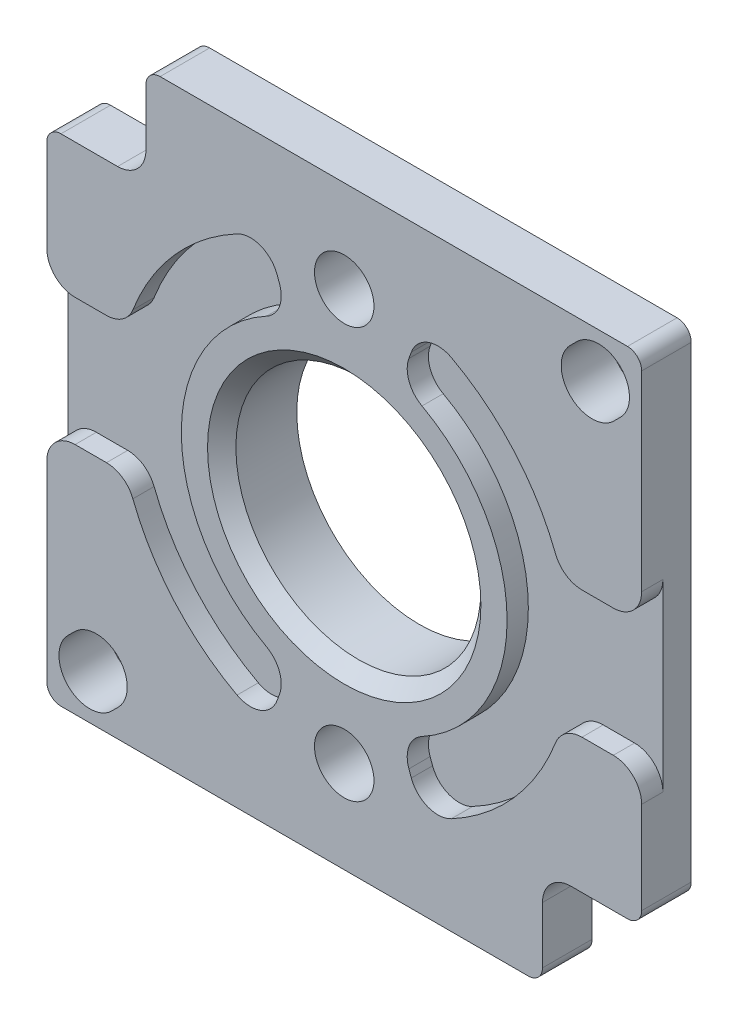
SolidWorks part; units mm, degrees
ref_plane "Front Plane" through (0, 0, 0) normal (0, 0, 1) x (1, 0, 0)
ref_plane "Top Plane" through (0, 0, 0) normal (0, 1, 0) x (1, 0, 0)
ref_plane "Right Plane" through (0, 0, 0) normal (1, 0, 0) x (0, 0, -1)
ref_plane "Plane1" through (0, 0, 1.75) normal (0, 0, 1) x (1, 0, 0)
sketch "Sketch1" plane through (0, 0, 1.75) normal (0, 0, 1) x (1, 0, 0)
  line L0 (-21, 21) -> (-21, -21)
  line L1 (-21, -21) -> (21, -21)
  line L2 (21, -21) -> (21, 21)
  line L3 (21, 21) -> (-21, 21)
extrude "Boss-Extrude1" add sketch "Sketch1" against normal blind 3.5
sketch "Sketch2" plane through (0, 0, 1.75) normal (0, 0, 1) x (1, 0, 0)
  line L0 (21, 4.5) -> (15.3542, 4.5)
  line L1 (5.4723, 15.0351) -> (3.9332, 10.8065)
  line L2 (3.9332, -10.8065) -> (5.4723, -15.0351)
  line L3 (15.3542, -4.5) -> (21, -4.5)
  line L4 (21, -4.5) -> (21, 4.5)
  arc A0 (15.3542, 4.5) -> (5.4723, 15.0351) centre (0, 0) ccw
  arc A1 (3.9332, 10.8065) -> (3.9332, -10.8065) centre (0, 0) cw
  arc A2 (5.4723, -15.0351) -> (15.3542, -4.5) centre (0, 0) ccw
extrude "Cut-Extrude1" cut sketch "Sketch2" against normal blind 1.5
sketch "Sketch3" plane through (0, 0, 1.75) normal (0, 0, 1) x (1, 0, 0)
  line L0 (-21, -4.5) -> (-15.3542, -4.5)
  line L1 (-5.4723, -15.0351) -> (-3.9332, -10.8065)
  line L2 (-3.9332, 10.8065) -> (-5.4723, 15.0351)
  line L3 (-15.3542, 4.5) -> (-21, 4.5)
  line L4 (-21, 4.5) -> (-21, -4.5)
  arc A0 (-15.3542, -4.5) -> (-5.4723, -15.0351) centre (0, 0) ccw
  arc A1 (-3.9332, -10.8065) -> (-3.9332, 10.8065) centre (0, 0) cw
  arc A2 (-5.4723, 15.0351) -> (-15.3542, 4.5) centre (0, 0) ccw
extrude "Cut-Extrude2" cut sketch "Sketch3" against normal blind 1.5
sketch "Sketch4" plane through (0, 0, -1.75) normal (0, 0, -1) x (-1, 0, 0)
  line L0 (-14, -21) -> (-14, -14)
  line L1 (-14, -14) -> (-21, -14)
  line L2 (-21, -14) -> (-21, -21)
  line L3 (-21, -21) -> (-14, -21)
extrude "Cut-Extrude3" cut sketch "Sketch4" against normal through all
sketch "Sketch5" plane through (0, 0, -1.75) normal (0, 0, -1) x (-1, 0, 0)
  line L0 (14, 21) -> (14, 14)
  line L1 (14, 14) -> (21, 14)
  line L2 (21, 14) -> (21, 21)
  line L3 (21, 21) -> (14, 21)
extrude "Cut-Extrude4" cut sketch "Sketch5" against normal through all
sketch "Sketch6" plane through (0, 0, 1.75) normal (0, 0, 1) x (1, 0, 0)
  line L0 (19.0415, 15.9585) -> (19.502, 16.419)
  line L1 (16.419, 19.502) -> (15.9585, 19.0415)
  arc A0 (15.9585, 19.0415) -> (19.0415, 15.9585) centre (17.5, 17.5) ccw
  arc A1 (19.502, 16.419) -> (16.419, 19.502) centre (17.9605, 17.9605) ccw
extrude "Cut-Extrude5" cut sketch "Sketch6" against normal through all
sketch "Sketch7" plane through (0, 0, -1.75) normal (0, 0, -1) x (-1, 0, 0)
  line L0 (19.502, -16.419) -> (19.0415, -15.9585)
  line L1 (15.9585, -19.0415) -> (16.419, -19.502)
  arc A0 (16.419, -19.502) -> (19.502, -16.419) centre (17.9605, -17.9605) ccw
  arc A1 (19.0415, -15.9585) -> (15.9585, -19.0415) centre (17.5, -17.5) ccw
extrude "Cut-Extrude6" cut sketch "Sketch7" against normal through all
sketch "Sketch8" plane through (0, 0, -1.75) normal (0, 0, -1) x (-1, 0, 0)
  arc A0 (-3.7492, -14.4206) -> (-3.7492, 14.4206) centre (0, 0) cw
  arc A1 (-3.7492, 14.4206) -> (3.7492, 14.4206) centre (0, 14.5) ccw
  arc A2 (3.7492, 14.4206) -> (3.7492, -14.4206) centre (0, 0) cw
  arc A3 (3.7492, -14.4206) -> (-3.7492, -14.4206) centre (0, -14.5) ccw
extrude "Boss-Extrude2" add sketch "Sketch8" along normal blind 1.8
sketch "Sketch9" plane through (0, 0, -3.55) normal (0, 0, -1) x (-1, 0, 0)
  line L0 (12.18, -5.5863) -> (9.1747, -4.3415)
  arc A0 (4.8505, -12.4913) -> (12.18, -5.5863) centre (0, 0) ccw
  arc A1 (9.1747, -4.3415) -> (4.1203, -9.2761) centre (0, 0) cw
  arc A2 (4.1203, -9.2761) -> (3.802, -10.8796) centre (4.5262, -10.19) ccw
  arc A3 (3.802, -10.8796) -> (4.8505, -12.4913) centre (0, -14.5) cw
extrude "Cut-Extrude7" cut sketch "Sketch9" against normal blind 1.8
sketch "Sketch10" plane through (0, 0, -3.55) normal (0, 0, -1) x (-1, 0, 0)
  line L0 (-9.1747, -4.3415) -> (-12.18, -5.5863)
  arc A0 (-12.18, -5.5863) -> (-4.8505, -12.4913) centre (0, 0) ccw
  arc A1 (-4.8505, -12.4913) -> (-3.802, -10.8796) centre (0, -14.5) cw
  arc A2 (-3.802, -10.8796) -> (-4.1203, -9.2761) centre (-4.5262, -10.19) ccw
  arc A3 (-4.1203, -9.2761) -> (-9.1747, -4.3415) centre (0, 0) cw
extrude "Cut-Extrude8" cut sketch "Sketch10" against normal blind 1.8
sketch "Sketch11" plane through (0, 0, -3.55) normal (0, 0, -1) x (-1, 0, 0)
  line L0 (-12.18, 5.5863) -> (-9.1747, 4.3415)
  arc A0 (-4.8505, 12.4913) -> (-12.18, 5.5863) centre (0, 0) ccw
  arc A1 (-9.1747, 4.3415) -> (-4.1203, 9.2761) centre (0, 0) cw
  arc A2 (-4.1203, 9.2761) -> (-3.802, 10.8796) centre (-4.5262, 10.19) ccw
  arc A3 (-3.802, 10.8796) -> (-4.8505, 12.4913) centre (0, 14.5) cw
extrude "Cut-Extrude9" cut sketch "Sketch11" against normal blind 1.8
sketch "Sketch12" plane through (0, 0, -3.55) normal (0, 0, -1) x (-1, 0, 0)
  line L0 (9.1747, 4.3415) -> (12.18, 5.5863)
  arc A0 (4.1203, 9.2761) -> (9.1747, 4.3415) centre (0, 0) cw
  arc A1 (12.18, 5.5863) -> (4.8505, 12.4913) centre (0, 0) ccw
  arc A2 (4.8505, 12.4913) -> (3.802, 10.8796) centre (0, 14.5) cw
  arc A3 (3.802, 10.8796) -> (4.1203, 9.2761) centre (4.5262, 10.19) ccw
extrude "Cut-Extrude10" cut sketch "Sketch12" against normal blind 1.8
sketch "Sketch13" plane through (0, 0, -3.55) normal (0, 0, -1) x (-1, 0, 0)
  line L0 (9.5573, -3.4176) -> (12.5627, -4.6624)
  line L1 (12.5627, 4.6624) -> (9.5573, 3.4176)
  arc A0 (12.5627, -4.6624) -> (12.5627, 4.6624) centre (0, 0) ccw
  arc A1 (9.5573, 3.4176) -> (9.5573, -3.4176) centre (0, 0) cw
extrude "Cut-Extrude11" cut sketch "Sketch13" against normal blind 1.8
sketch "Sketch14" plane through (0, 0, -3.55) normal (0, 0, -1) x (-1, 0, 0)
  line L0 (-12.5627, -4.6624) -> (-9.5573, -3.4176)
  line L1 (-9.5573, 3.4176) -> (-12.5627, 4.6624)
  arc A0 (-12.5627, 4.6624) -> (-12.5627, -4.6624) centre (0, 0) ccw
  arc A1 (-9.5573, -3.4176) -> (-9.5573, 3.4176) centre (0, 0) cw
extrude "Cut-Extrude12" cut sketch "Sketch14" against normal blind 1.8
hole_wizard "Ø4.2 (4.2) Diameter Hole1" positions "Sketch16" profile "Sketch15" hole size "Ø4.2" standard "ANSI Metric"
sketch "Sketch16" plane through (0, 0, 1.75) normal (0, 0, 1) x (1, 0, 0)
  point P0 (0, 14.5)
  point P1 (0, -14.5)
sketch "Sketch15" plane through (0, 14.5, 1.75) normal (1, 0, 0) x (0, -1, 0)
  line L0 (0, 0) -> (0, 5.3)
  line L1 (0, 5.3) -> (2.1, 5.3)
  line L2 (2.1, 5.3) -> (2.1, 0)
  line L5 (2.1, 0) -> (0, 0)
  line L11 (0, -6.35) -> (0, 107.95) construction
  dimension "Thru Hole Dia." = 4.2
  dimension "Thru Hole Depth" = 5.3
hole_wizard "M16 Clearance Hole1" positions "Sketch18" profile "Sketch17" hole size "M16" standard "ANSI Metric"
sketch "Sketch18" plane through (0, 0, 1.75) normal (0, 0, 1) x (1, 0, 0)
  point P0 (0, 0)
sketch "Sketch17" plane through (0, 0, 1.75) normal (1, 0, 0) x (0, -1, 0)
  line L0 (0, 0) -> (0, 5.3)
  line L1 (0, 5.3) -> (8.65, 5.3)
  line L2 (8.65, 5.3) -> (8.65, 0)
  line L5 (8.65, 0) -> (0, 0)
  line L11 (0, -6.35) -> (0, 107.95) construction
  dimension "Thru Hole Dia." = 17.3
  dimension "Thru Hole Depth" = 5.3
fillet "Fillet1" radius 1 30 edges at (12.5627, 4.6624, -2.65) (14, -21, 0) (21, 21, 0) (-12.18, 5.5863, -2.65) (-12.5627, -4.6624, -2.65) (9.1747, 4.3415, -2.65) (-12.5627, 4.6624, -2.65) (-21, 14, 0) (-9.5573, 3.4176, -2.65) (12.18, 5.5863, -2.65) (-4.8505, 12.4913, -2.65) (-9.5573, -3.4176, -2.65) (9.5573, 3.4176, -2.65) (-9.1747, -4.3415, -2.65) (21, -14, 0) (-12.18, -5.5863, -2.65) (-14, 21, 0) (-4.8505, -12.4913, -2.65) (-21, -21, 0) (12.18, -5.5863, -2.65) (4.8505, 12.4913, -2.65) (4.8505, -12.4913, -2.65) (9.1747, -4.3415, -2.65) (9.5573, -3.4176, -2.65) (12.5627, -4.6624, -2.65) (-9.1747, 4.3415, -2.65) (-3.7492, -14.4206, -2.65) (3.7492, 14.4206, -2.65) (3.7492, -14.4206, -2.65) (-3.7492, 14.4206, -2.65)
chamfer "Chamfer1" distance 0.5 angle 45 8 edges at (0, 10.75, -3.55) (-4.094, 14.0247, -3.55) (-14.9, 0, -3.55) (4.094, 14.0247, -3.55) (14.9, 0, -3.55) (-4.094, -14.0247, -3.55) (4.094, -14.0247, -3.55) (0, -10.75, -3.55)
chamfer "Chamfer2" distance 1 angle 45 1 edges at (8.65, 0, 1.75)
fillet "Fillet2" radius 2 18 edges at (-21, -4.5, 1) (-3.9332, 10.8065, 1) (-15.3542, 4.5, 1) (21, -4.5, 1) (-5.4723, -15.0351, 1) (15.3542, -4.5, 1) (-14, 14, 0) (5.4723, -15.0351, 1) (-5.4723, 15.0351, 1) (3.9332, 10.8065, 1) (-3.9332, -10.8065, 1) (5.4723, 15.0351, 1) (-15.3542, -4.5, 1) (15.3542, 4.5, 1) (14, -14, 0) (21, 4.5, 1) (-21, 4.5, 1) (3.9332, -10.8065, 1)
